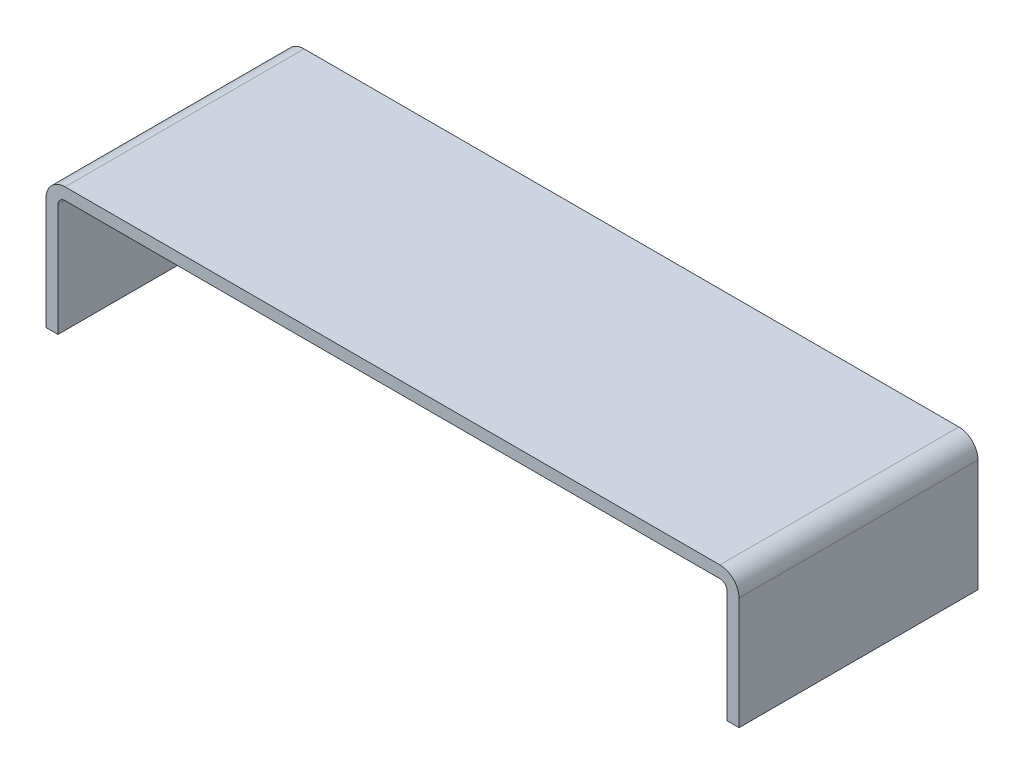
SolidWorks part; units mm, degrees
ref_plane "Front Plane" through (0, 0, 0) normal (0, 0, 1) x (1, 0, 0)
ref_plane "Top Plane" through (0, 0, 0) normal (0, 1, 0) x (1, 0, 0)
ref_plane "Right Plane" through (0, 0, 0) normal (1, 0, 0) x (0, 0, -1)
sketch "Sketch1" plane through (0, 0, 0) normal (0, 0, 1) x (1, 0, 0)
  line L0 (-35.56, -12.7) -> (-35.56, -0.762)
  line L1 (-34.798, 0) -> (34.798, 0)
  line L2 (35.56, -0.762) -> (35.56, -12.7)
  arc A0 (34.798, 0) -> (35.56, -0.762) centre (34.798, -0.762) cw
  arc A1 (-35.56, -0.762) -> (-34.798, 0) centre (-34.798, -0.762) cw
  point P2 (0, 0)
  point P8 (35.56, 0)
  point P11 (-35.56, 0)
  dimension "D3" = 0.762
  dimension "D1" = 12.7
  dimension "D2" = 71.12
extrude "Extrude-Thin1" add sketch "Sketch1" along normal mid plane 25.4 thin thin type one direction reverse wall 1.27
